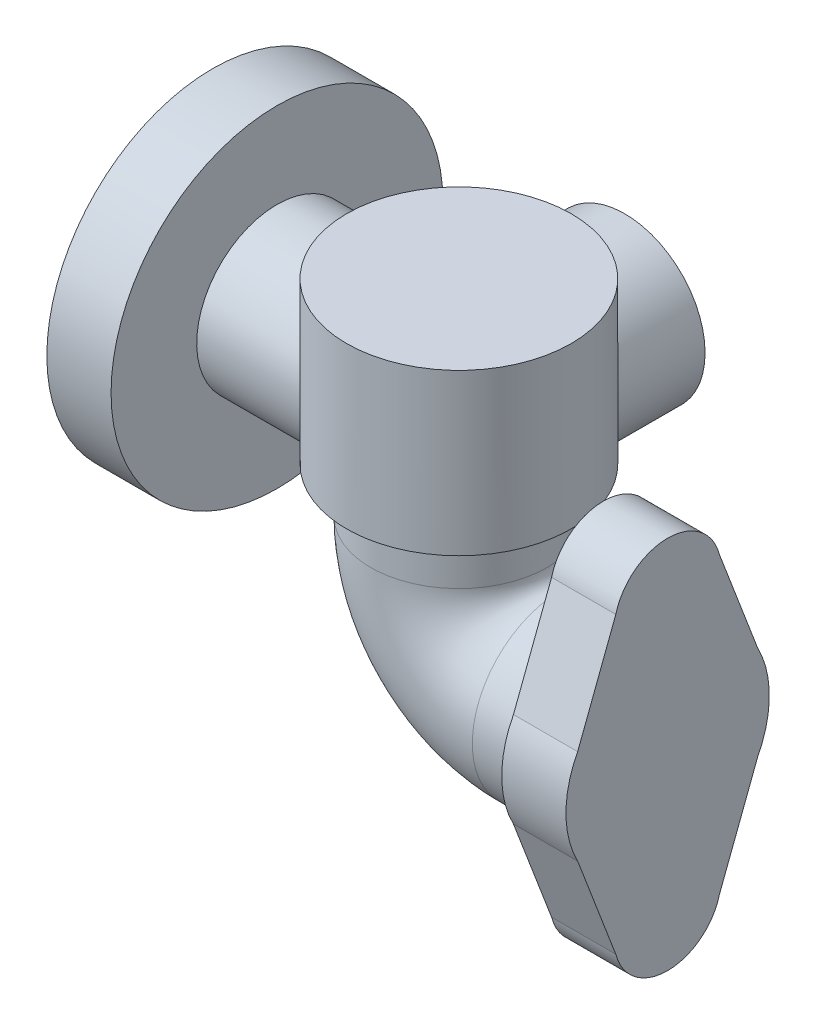
SolidWorks part; units mm, degrees
ref_plane "Front Plane" through (0, 0, 0) normal (0, 0, 1) x (1, 0, 0)
ref_plane "Top Plane" through (0, 0, 0) normal (0, 1, 0) x (1, 0, 0)
ref_plane "Right Plane" through (0, 0, 0) normal (1, 0, 0) x (0, 0, -1)
sketch "Sketch1" plane through (0, 0, 0) normal (0, 0, 1) x (1, 0, 0)
  line L0 (0, 0) -> (-92, 0) construction
  line L1 (-92, 0) -> (-92, 62)
  line L4 (-92, 62) -> (-68, 62)
  line L7 (-68, 62) -> (-68, 30)
  line L9 (-68, 30) -> (0, 30)
  line L10 (0, 30) -> (0, 0)
  line L12 (0, 0) -> (-92, 0)
revolve "Revolve1" add sketch "Sketch1" angle 360 about L0
sketch "Sketch2" plane through (0, 0, 0) normal (1, 0, 0) x (0, 0, -1)
  line L0 (0, 40) -> (0, -20)
  line L1 (0, 40) -> (42, 40)
  line L2 (0, 40) -> (0, -40) construction
  line L4 (42, 40) -> (42, -20)
  line L5 (42, 40) -> (42, -20)
  line L6 (0, -20) -> (42, -20)
  point P0 (21, 0)
  dimension "D1" = 42
revolve "Revolve2" add sketch "Sketch2" angle 360 about L2
sketch "Sketch3" plane through (0, -20, 0) normal (0, -1, 0) x (1, 0, 0)
  circle A0 centre (0, 0) radius 33
  arc A1 (-35.5528, -22.3607) -> (-35.5528, 22.3607) centre (0, 0) ccw construction
sketch "Sketch4" plane through (0, 0, 0) normal (0, 0, 1) x (1, 0, 0)
  line L0 (0, -20) -> (0, -37)
  line L1 (38, -75) -> (78, -75)
  arc A0 (0, -37) -> (38, -75) centre (38, -37) ccw
sweep "Sweep1" add profiles "Sketch3" path "Sketch4"
sketch "Sketch5" plane through (78, 0, 0) normal (1, 0, 0) x (0, 0, -1)
  line L2 (-19.3649, -20) -> (-33.6166, -57.282)
  line L3 (-33, -20) -> (33, -20) construction
  line L4 (19.3649, -20) -> (33.6166, -57.282)
  line L6 (19.3649, -130) -> (33.6166, -92.718)
  line L7 (-19.3649, -130) -> (-33.6166, -92.718)
  arc A0 (33.6166, -92.718) -> (33.6166, -57.282) centre (0, -75) ccw
  arc A1 (19.3649, -20) -> (-19.3649, -20) centre (0, -25) ccw
  arc A3 (-19.3649, -130) -> (19.3649, -130) centre (0, -125) ccw
  arc A4 (-33.6166, -57.282) -> (-33.6166, -92.718) centre (0, -75) ccw
extrude "Boss-Extrude1" add sketch "Sketch5" against normal blind 24
ref_plane "Plane1" through (0, 0, 0) normal (1, 0, 0) x (0, 0, -1)
sketch "Sketch6" plane through (0, 0, 0) normal (1, 0, 0) x (0, 0, -1)
  line L0 (0, 0) -> (62, 0)
  line L1 (0, 0) -> (62, 0) construction
  line L2 (0, 0) -> (0, 30)
  line L3 (0, 30) -> (62, 30)
  line L4 (62, 0) -> (62, 30)
revolve "Revolve3" add sketch "Sketch6" angle 360 about L1
